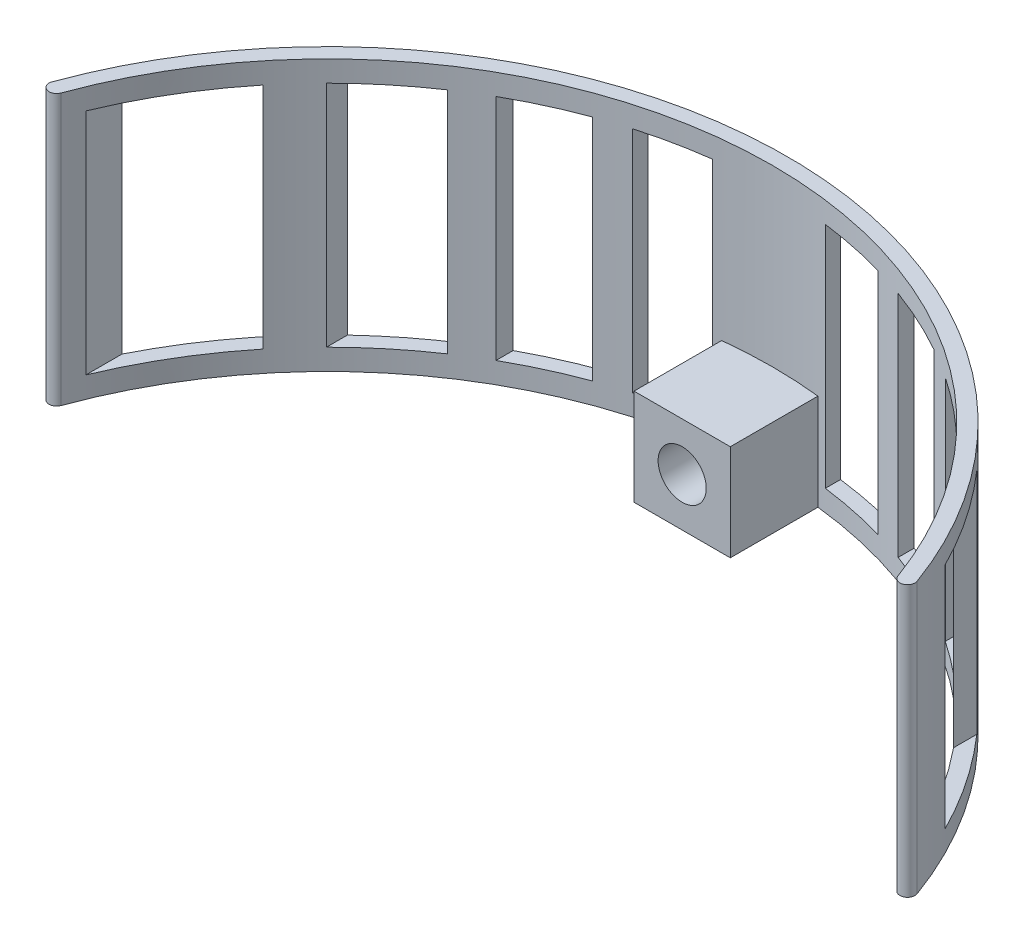
SolidWorks part; units mm, degrees
ref_plane "Front Plane" through (0, 0, 0) normal (0, 0, 1) x (1, 0, 0)
ref_plane "Top Plane" through (0, 0, 0) normal (0, 1, 0) x (1, 0, 0)
ref_plane "Right Plane" through (0, 0, 0) normal (1, 0, 0) x (0, 0, -1)
sketch "Sketch1" plane through (0, 0, 0) normal (0, 1, 0) x (1, 0, 0)
  line L0 (0, 0) -> (139.0745, 50.619) construction
  line L1 (0, 0) -> (-139.0745, 50.619) construction
  line L2 (-60.424, 0) -> (78.8018, 0) construction
  line L3 (0, 64.3223) -> (0, -69.3344) construction
  arc A0 (139.0745, 50.619) -> (-139.0745, 50.619) centre (0, 0) ccw
  arc A1 (143.773, 52.3291) -> (-143.773, 52.3291) centre (0, 0) ccw
  arc A2 (139.0745, 50.619) -> (143.773, 52.3291) centre (141.4237, 51.474) ccw
  arc A3 (-139.0745, 50.619) -> (-143.773, 52.3291) centre (-141.4237, 51.474) cw
  dimension "D4" = 148
  dimension "D1" = 20
  dimension "D2" = 20
  dimension "D3" = 5
extrude "Boss-Extrude1" add sketch "Sketch1" along normal blind 90
sketch "Sketch2" plane through (0, 0, 0) normal (0, 0, 1) x (1, 0, 0)
  line L0 (-139.0745, 0) -> (139.0745, 0) construction
  line L1 (-16, 0) -> (16, 0)
  line L2 (-16, 0) -> (-16, 32)
  line L3 (-16, 32) -> (16, 32)
  line L4 (16, 0) -> (16, 32)
  line L5 (0, 0) -> (0, 116.7176) construction
  circle A0 centre (0, 16) radius 8
  point P11 (0, 17.2272)
  dimension "D1" = 16
  dimension "D2" = 16
  dimension "D3" = 16
extrude "Boss-Extrude2" add sketch "Sketch2" against normal up to next
sketch "Sketch3" plane through (0, 0, 0) normal (0, 0, 1) x (1, 0, 0)
  circle A0 centre (0, 16) radius 8 construction
  circle A1 centre (0, 16) radius 8
extrude "Cut-Extrude1" cut sketch "Sketch3" against normal blind 210
sketch "Sketch4" plane through (0, 32, 0) normal (0, 1, 0) x (1, 0, 0)
  line L0 (16, 147.1326) -> (16, 0) construction
  line L1 (-16, 0) -> (16, 0)
  line L2 (-16, 0) -> (-16, 118)
  line L3 (-16, 118) -> (16, 118)
  line L4 (16, 0) -> (16, 118)
  arc A1 (139.0745, 50.619) -> (-139.0745, 50.619) centre (0, 0) ccw construction
  point P10 (0, 148)
  dimension "D1" = 30
extrude "Cut-Extrude2" cut sketch "Sketch4" against normal blind 210
ref_plane "Plane1" through (0, 0, -153) normal (0, 0, -1) x (-1, 0, 0)
sketch "Sketch5" plane through (0, 0, -153) normal (0, 0, -1) x (-1, 0, 0)
  line L0 (143.773, 90) -> (-143.773, 90) construction
  line L1 (-136.773, 83) -> (-114.773, 83)
  line L2 (-136.773, 83) -> (-136.773, 7)
  line L3 (-136.773, 7) -> (-114.773, 7)
  line L4 (-114.773, 83) -> (-114.773, 7)
  line L5 (-104.773, 83) -> (-82.773, 83)
  line L6 (-104.773, 83) -> (-104.773, 7)
  line L7 (-104.773, 7) -> (-82.773, 7)
  line L8 (-82.773, 83) -> (-82.773, 7)
  line L9 (-72.773, 83) -> (-50.773, 83)
  line L10 (-72.773, 83) -> (-72.773, 7)
  line L11 (-72.773, 7) -> (-50.773, 7)
  line L14 (-50.773, 83) -> (-50.773, 7)
  line L17 (18.773, 83) -> (40.773, 83)
  line L18 (18.773, 83) -> (18.773, 7)
  line L19 (18.773, 7) -> (40.773, 7)
  line L20 (40.773, 83) -> (40.773, 7)
  line L21 (50.773, 83) -> (72.773, 83)
  line L22 (50.773, 83) -> (50.773, 7)
  line L23 (50.773, 7) -> (72.773, 7)
  line L24 (72.773, 83) -> (72.773, 7)
  line L25 (82.773, 83) -> (104.773, 83)
  line L26 (82.773, 83) -> (82.773, 7)
  line L27 (82.773, 7) -> (104.773, 7)
  line L28 (104.773, 83) -> (104.773, 7)
  line L29 (114.773, 83) -> (136.773, 83)
  line L30 (114.773, 83) -> (114.773, 7)
  line L31 (114.773, 7) -> (136.773, 7)
  line L32 (136.773, 83) -> (136.773, 7)
  line L37 (-40.773, 83) -> (-18.773, 83)
  line L38 (-40.773, 83) -> (-40.773, 7)
  line L39 (-40.773, 7) -> (-18.773, 7)
  line L40 (-18.773, 83) -> (-18.773, 7)
  line L41 (-143.773, 0) -> (143.773, 0) construction
  line L42 (-143.773, 90) -> (-143.773, 0) construction
  line L43 (143.773, 90) -> (143.773, 0) construction
  point P36 (-93.773, 83)
  dimension "D1" = 7
  dimension "D2" = 7
  dimension "D3" = 22
  dimension "D4" = 7
  dimension "D5" = 22
  dimension "D6" = 22
  dimension "D7" = 22
  dimension "D8" = 22
  dimension "D9" = 22
  dimension "D10" = 22
  dimension "D11" = 22
  dimension "D12" = 7
  dimension "D13" = 10
  dimension "D14" = 10
  dimension "D15" = 10
  dimension "D16" = 10
  dimension "D17" = 10
  dimension "D18" = 10
extrude "Cut-Extrude4" cut sketch "Sketch5" against normal blind 210
